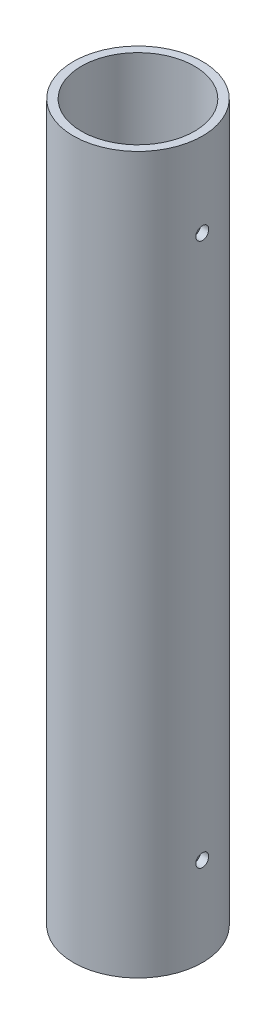
SolidWorks part; units mm, degrees
material "Default"
ref_plane "Front Plane" through (0, 0, 0) normal (0, 0, 1) x (1, 0, 0)
ref_plane "Top Plane" through (0, 0, 0) normal (0, 1, 0) x (1, 0, 0)
ref_plane "Right Plane" through (0, 0, 0) normal (1, 0, 0) x (0, 0, -1)
sketch "Sketch2" plane through (0, 0, 0) normal (0, 1, 0) x (1, 0, 0)
  circle A0 centre (0, 0) radius 8
  circle A1 centre (0, 0) radius 7
extrude "Boss-Extrude2" add sketch "Sketch2" along normal blind 88.6953 contours A0 | A1
ref_point "Point1"
ref_plane "Plane1" through (8, 0, 0) normal (1, 0, 0) x (0, 0, -1)
sketch "Sketch4" plane through (8, 0, 0) normal (1, 0, 0) x (0, 0, -1)
  line L0 (0, 0) -> (0, 11) construction
  circle A0 centre (0, 11) radius 1
  dimension "D1" = 11
sketch "Sketch5" plane through (8, 0, 0) normal (1, 0, 0) x (0, 0, -1)
  line L0 (0, 88.6953) -> (0, 78.2792) construction
  line L1 (7, 88.6953) -> (-7, 88.6953) construction
  circle A0 centre (0, 78.2792) radius 1
  dimension "D1" = 10.4161
hole_wizard "M2 Tapped Hole1" positions "Sketch6" profile "Sketch7" tap size "M2" standard "ISO" end condition through all
sketch "Sketch6" plane through (8, 0, 0) normal (1, 0, 0) x (0, 0, -1)
  point P0 (0, 78.2792)
sketch "Sketch7" plane through (8, 78.2792, 0) normal (0, 1, 0) x (0, 0, -1)
  line L0 (0, 0) -> (0, 16)
  line L1 (0, 16) -> (0.8, 16)
  line L2 (0.8, 16) -> (0.8, 0)
  line L5 (0.8, 0) -> (0, 0)
  line L11 (0, -6.35) -> (0, 107.95) construction
  dimension "Thru Tap Drill Dia." = 1.6
  dimension "Thru Tap Drill Depth" = 16
cosmetic thread "Hole Thread1" parameters "D2"=2
hole_wizard "M2 Tapped Hole2" positions "Sketch8" profile "Sketch9" tap size "M2" standard "ISO" end condition through all
sketch "Sketch8" plane through (8, 0, 0) normal (1, 0, 0) x (0, 0, -1)
  point P0 (0, 11)
sketch "Sketch9" plane through (8, 11, 0) normal (0, 1, 0) x (0, 0, -1)
  line L0 (0, 0) -> (0, 16)
  line L1 (0, 16) -> (0.8, 16)
  line L2 (0.8, 16) -> (0.8, 0)
  line L5 (0.8, 0) -> (0, 0)
  line L11 (0, -6.35) -> (0, 107.95) construction
  dimension "Thru Tap Drill Dia." = 1.6
  dimension "Thru Tap Drill Depth" = 16
cosmetic thread "Hole Thread2" parameters "D2"=2
